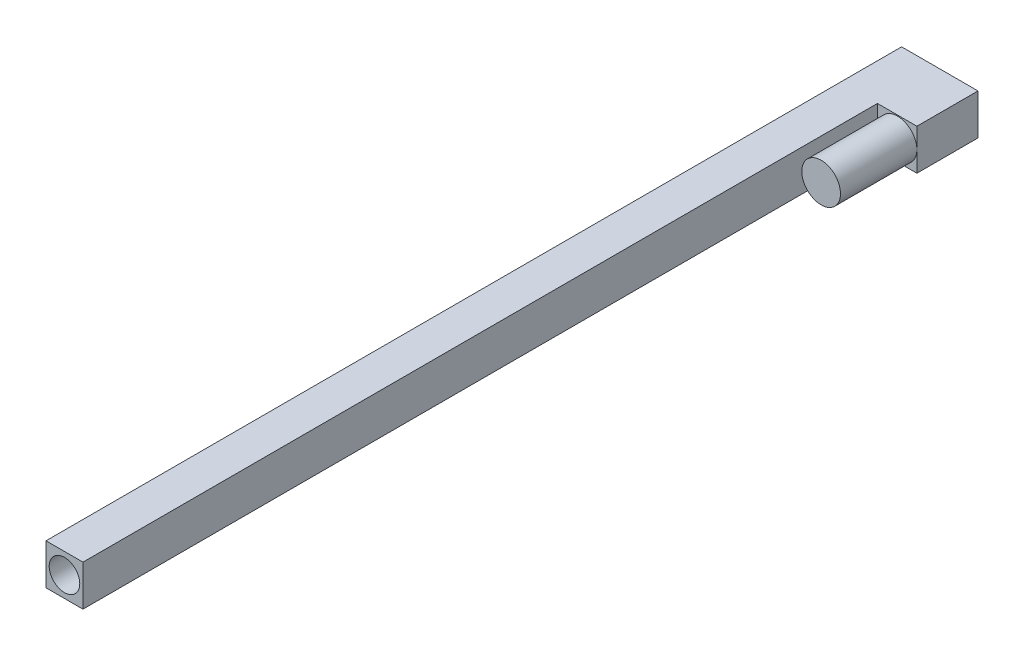
SolidWorks part; units mm, degrees
ref_plane "前基準面" through (0, 0, 0) normal (0, 0, 1) x (1, 0, 0)
ref_plane "上基準面" through (0, 0, 0) normal (0, 1, 0) x (1, 0, 0)
ref_plane "右基準面" through (0, 0, 0) normal (1, 0, 0) x (0, 0, -1)
sketch "草圖1" plane through (0, 0, 0) normal (0, 0, 1) x (1, 0, 0)
  line L1 (-44.3742, 18.8936) -> (30.6258, 18.8936)
  line L2 (-44.3742, 18.8936) -> (-44.3742, -21.1064)
  line L3 (-44.3742, -21.1064) -> (30.6258, -21.1064)
  line L4 (30.6258, 18.8936) -> (30.6258, -21.1064)
  dimension "D1" = 40
  dimension "D2" = 75
extrude "填料-伸長1" add sketch "草圖1" along normal blind 60
sketch "草圖2" plane through (0, 0, 60) normal (0, 0, 1) x (1, 0, 0)
  line L3 (30.6258, -21.1064) -> (30.6258, 18.8936) construction
  circle A0 centre (11.6258, -1.0257) radius 19
  dimension "D1" = 38
extrude "填料-伸長2" add sketch "草圖2" along normal blind 75
sketch "草圖3" plane through (0, 0, 60) normal (0, 0, 1) x (1, 0, 0)
  line L0 (-44.3742, -21.1064) -> (30.6258, -21.1064) construction
  line L1 (-44.3742, 18.8936) -> (-8.0844, 18.8936)
  line L2 (-44.3742, 18.8936) -> (-44.3742, -21.1064)
  line L3 (-44.3742, -21.1064) -> (-8.0844, -21.1064)
  line L4 (-8.0844, 18.8936) -> (-8.0844, -21.1064)
extrude "填料-伸長3" add sketch "草圖3" along normal blind 780
sketch "草圖7" plane through (0, 0, 840) normal (0, 0, 1) x (1, 0, 0)
  circle A0 centre (-26.2293, -1.1064) radius 15
  dimension "D1" = 30
extrude "除料-伸長1" cut sketch "草圖7" against normal blind 800
